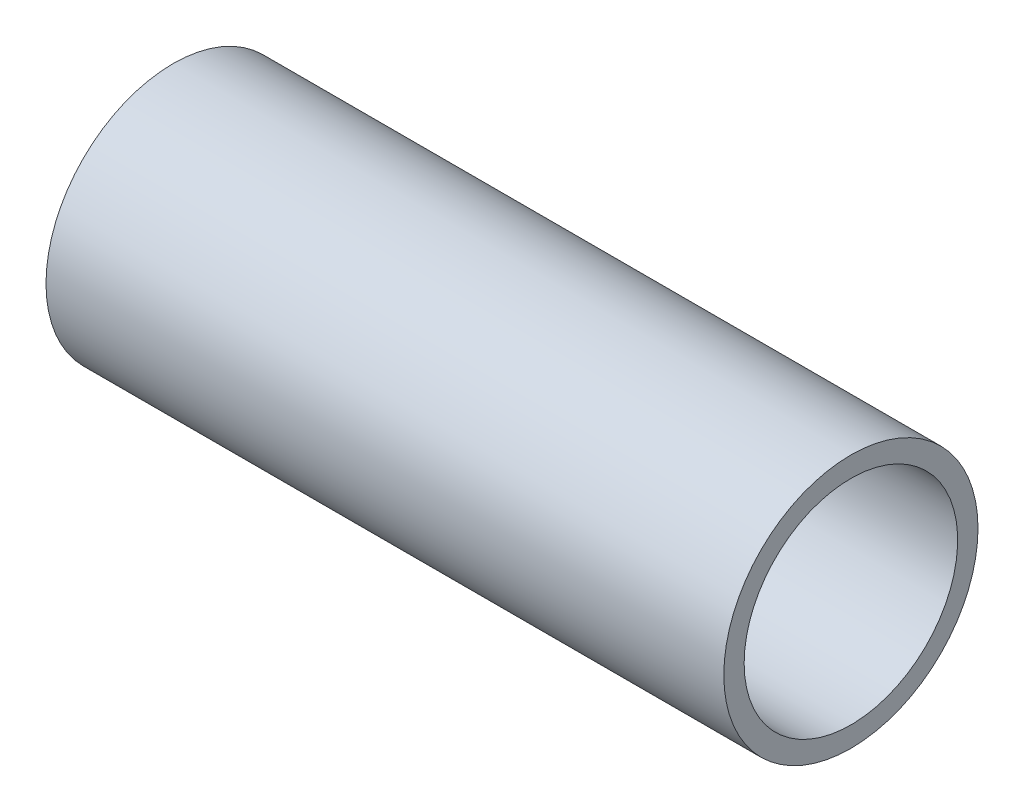
SolidWorks part; units mm, degrees
ref_plane "Front Plane" through (0, 0, 0) normal (0, 0, 1) x (1, 0, 0)
ref_plane "Top Plane" through (0, 0, 0) normal (0, 1, 0) x (1, 0, 0)
ref_plane "Right Plane" through (0, 0, 0) normal (1, 0, 0) x (0, 0, -1)
sketch "Sketch1" plane through (0, 0, 0) normal (1, 0, 0) x (0, 0, -1)
  circle A0 centre (0, 0) radius 9.525
  dimension "D1" = 19.05
extrude "Boss-Extrude1" add sketch "Sketch1" along normal blind 50.8
sketch "Sketch3" plane through (0, 0, 0) normal (-1, 0, 0) x (0, 0, 1)
  circle A0 centre (0, 0) radius 8.509
  dimension "D1" = 17.018
extrude "Cut-Extrude1" cut sketch "Sketch3" against normal blind 1.524
sketch "Sketch4" plane through (1.524, 0, 0) normal (-1, 0, 0) x (0, 0, 1)
  circle A0 centre (0, 0) radius 8.001
  dimension "D1" = 16.002
extrude "Cut-Extrude2" cut sketch "Sketch4" against normal through all
